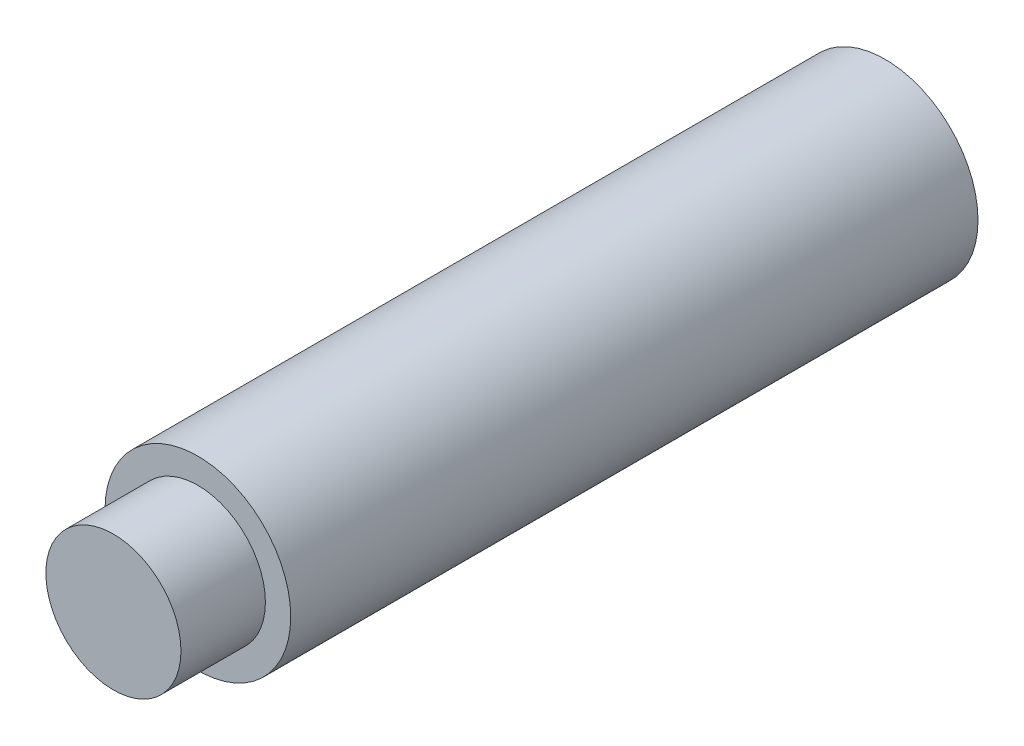
SolidWorks part; units mm, degrees
ref_plane "Front Plane" through (0, 0, 0) normal (0, 0, 1) x (1, 0, 0)
ref_plane "Top Plane" through (0, 0, 0) normal (0, 1, 0) x (1, 0, 0)
ref_plane "Right Plane" through (0, 0, 0) normal (1, 0, 0) x (0, 0, -1)
sketch "Sketch1" plane through (0, 0, 0) normal (0, 0, 1) x (1, 0, 0)
  circle A0 centre (0, 0) radius 5.5
  dimension "D1" = 11
extrude "Boss-Extrude1" add sketch "Sketch1" along normal blind 40.7
sketch "Sketch2" plane through (0, 0, 40.7) normal (0, 0, 1) x (1, 0, 0)
  circle A0 centre (0, 0) radius 4
  dimension "D1" = 8
extrude "Boss-Extrude2" add sketch "Sketch2" along normal blind 5
cosmetic thread "Cosmetic Thread1" parameters "D1"=5, "D2"=7
hole_wizard "M6x1.0 Tapped Hole1" positions "Sketch4" profile "Sketch3" tap size "M6x1.0" standard "ANSI Metric"
sketch "Sketch4" plane through (0, 0, 0) normal (0, 0, -1) x (-1, 0, 0)
  point P0 (0, 0)
sketch "Sketch3" plane through (0, 0, 0) normal (1, 0, 0) x (0, 1, 0)
  line L0 (0, 0) -> (0, 8.5022)
  line L1 (0, 8.5022) -> (2.5, 7)
  line L2 (2.5, 7) -> (2.5, 0.525)
  line L3 (2.5, 0.525) -> (3.025, 0)
  line L5 (3.025, 0) -> (0, 0)
  line L6 (-2.5, 0.525) -> (-3.025, 0) construction
  line L10 (0, 8.5022) -> (-2.5, 7) construction
  line L11 (0, -6.35) -> (0, 107.95) construction
  dimension "Tap Drill Dia." = 5
  dimension "Tap Drill Depth" = 7
  dimension "Near C'Sink Dia." = 6.05
  dimension "Near C'Sink Angle" = 90
  dimension "Drill Angle" = 118
cosmetic thread "Hole Thread1"
